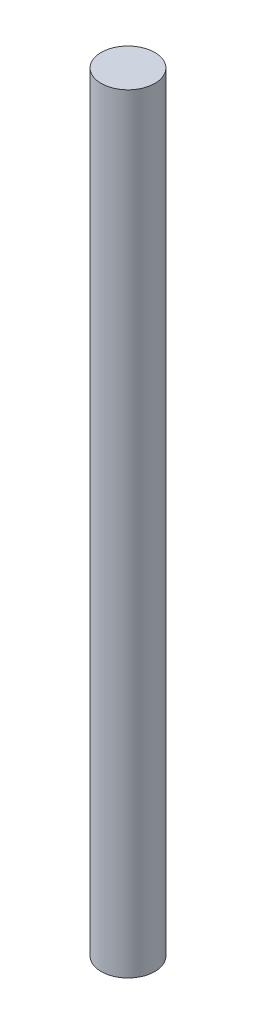
SolidWorks part; units mm, degrees
ref_plane "Front Plane" through (0, 0, 0) normal (0, 0, 1) x (1, 0, 0)
ref_plane "Top Plane" through (0, 0, 0) normal (0, 1, 0) x (1, 0, 0)
ref_plane "Right Plane" through (0, 0, 0) normal (1, 0, 0) x (0, 0, -1)
sketch "Sketch1" plane through (0, 0, 0) normal (0, 1, 0) x (1, 0, 0)
  circle A0 centre (0, 0) radius 0.75
  dimension "D1" = 1.5
extrude "Boss-Extrude1" add sketch "Sketch1" along normal blind 21.5
sketch "Sketch2" plane through (0, 0, 0) normal (0, 1, 0) x (1, 0, 0)
  circle A0 centre (0, 0) radius 0.95
  dimension "D1" = 1.9
extrude "Boss-Extrude2" [suppressed] add sketch "Sketch2" along normal blind 21.5
